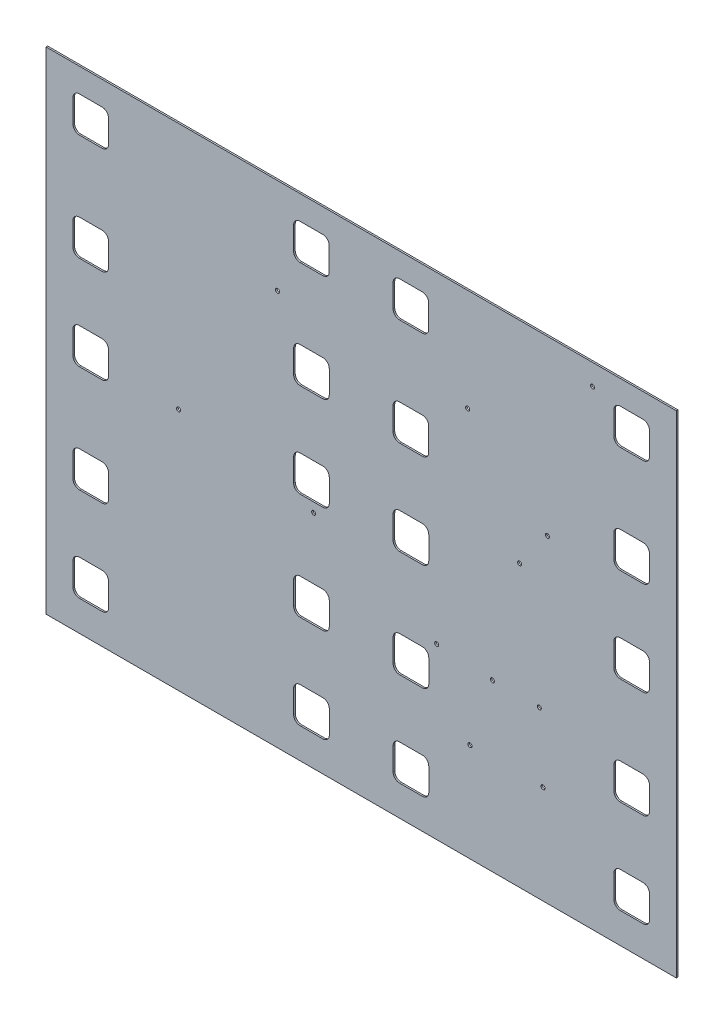
SolidWorks part; units mm, degrees
material "ABS"
ref_plane "X-Y Datum" through (0, 0, 0) normal (0, 0, 1) x (1, 0, 0)
ref_plane "X-Z Datum" through (0, 0, 0) normal (0, 1, 0) x (1, 0, 0)
ref_plane "Y-Z Datum" through (0, 0, 0) normal (1, 0, 0) x (0, 0, -1)
sketch "Sketch9" plane through (0, 0, 0) normal (0, 0, 1) x (1, 0, 0)
  line L0 (-82.7559, -182.5893) -> (-82.7583, -160.1613) construction
  line L1 (-89.109, -153.8119) -> (-111.537, -153.8143) construction
  line L2 (-117.8863, -160.165) -> (-117.8839, -182.593) construction
  line L3 (-111.5333, -188.9423) -> (-89.1053, -188.9399) construction
  line L4 (476.934, -311.4483) -> (476.8831, 172.8027)
  line L5 (476.8831, 172.8027) -> (-144.3755, 172.7375)
  line L6 (-144.3755, 172.7375) -> (-144.3246, -311.5135)
  line L7 (-144.3246, -311.5135) -> (476.934, -311.4483)
  line L8 (476.934, -311.4483) -> (476.8831, 172.8027)
  line L9 (476.8831, 172.8027) -> (-144.3755, 172.7375)
  line L10 (-144.3755, 172.7375) -> (-144.3246, -311.5135)
  line L11 (-144.3246, -311.5135) -> (476.934, -311.4483)
  line L12 (-111.5443, -83.8117) -> (-89.1163, -83.8093) construction
  line L13 (-82.767, -77.4587) -> (-82.7693, -55.0307) construction
  line L14 (-89.12, -48.6813) -> (-111.548, -48.6837) construction
  line L15 (-117.8973, -55.0344) -> (-117.895, -77.4624) construction
  line L16 (-82.7877, 120.2549) -> (-82.7901, 142.6829) construction
  line L17 (-89.1408, 149.0323) -> (-111.5688, 149.0299) construction
  line L18 (-117.9181, 142.6792) -> (-117.9157, 120.2512) construction
  line L19 (-111.5651, 113.9019) -> (-89.1371, 113.9043) construction
  line L20 (-111.554, 8.7713) -> (-89.126, 8.7737) construction
  line L21 (-117.9071, 37.5486) -> (-117.9047, 15.1206) construction
  line L22 (-89.1297, 43.9017) -> (-111.5577, 43.8993) construction
  line L23 (-82.7767, 15.1243) -> (-82.7791, 37.5523) construction
  line L24 (-82.7559, -182.5893) -> (-82.7583, -160.1613)
  line L25 (-89.109, -153.8119) -> (-111.537, -153.8143)
  line L26 (-117.8863, -160.165) -> (-117.8839, -182.593)
  line L27 (-111.5333, -188.9423) -> (-89.1053, -188.9399)
  line L28 (-111.5443, -83.8117) -> (-89.1163, -83.8093)
  line L29 (-82.767, -77.4587) -> (-82.7693, -55.0307)
  line L30 (-89.12, -48.6813) -> (-111.548, -48.6837)
  line L31 (-117.8973, -55.0344) -> (-117.895, -77.4624)
  line L32 (-82.7877, 120.2549) -> (-82.7901, 142.6829)
  line L33 (-89.1408, 149.0323) -> (-111.5688, 149.0299)
  line L34 (-117.9181, 142.6792) -> (-117.9157, 120.2512)
  line L35 (-111.5651, 113.9019) -> (-89.1371, 113.9043)
  line L36 (-111.554, 8.7713) -> (-89.126, 8.7737)
  line L37 (-117.9071, 37.5486) -> (-117.9047, 15.1206)
  line L38 (-89.1297, 43.9017) -> (-111.5577, 43.8993)
  line L39 (-82.7767, 15.1243) -> (-82.7791, 37.5523)
  line L40 (-82.7462, -275.1723) -> (-82.7486, -252.7443) construction
  line L41 (-89.0992, -246.3949) -> (-111.5272, -246.3973) construction
  line L42 (-117.8766, -252.748) -> (-117.8742, -275.176) construction
  line L43 (-111.5235, -281.5253) -> (-89.0955, -281.5229) construction
  line L44 (-82.7462, -275.1723) -> (-82.7486, -252.7443)
  line L45 (-89.0992, -246.3949) -> (-111.5272, -246.3973)
  line L46 (-117.8766, -252.748) -> (-117.8742, -275.176)
  line L47 (-111.5235, -281.5253) -> (-89.0955, -281.5229)
  arc A0 (-89.1053, -188.9399) -> (-82.7559, -182.5893) centre (-89.1059, -182.5899) ccw construction
  arc A1 (-82.7583, -160.1613) -> (-89.109, -153.8119) centre (-89.1083, -160.1619) ccw construction
  arc A2 (-111.537, -153.8143) -> (-117.8863, -160.165) centre (-111.5363, -160.1643) ccw construction
  arc A3 (-117.8839, -182.593) -> (-111.5333, -188.9423) centre (-111.5339, -182.5923) ccw construction
  arc A4 (-89.1163, -83.8093) -> (-82.767, -77.4587) centre (-89.117, -77.4593) ccw construction
  arc A5 (-82.7693, -55.0307) -> (-89.12, -48.6813) centre (-89.1193, -55.0313) ccw construction
  arc A6 (-111.548, -48.6837) -> (-117.8973, -55.0344) centre (-111.5473, -55.0337) ccw construction
  arc A7 (-117.895, -77.4624) -> (-111.5443, -83.8117) centre (-111.545, -77.4617) ccw construction
  arc A8 (-89.1371, 113.9043) -> (-82.7877, 120.2549) centre (-89.1377, 120.2543) ccw construction
  arc A9 (-82.7901, 142.6829) -> (-89.1408, 149.0323) centre (-89.1401, 142.6823) ccw construction
  arc A10 (-111.5688, 149.0299) -> (-117.9181, 142.6792) centre (-111.5681, 142.6799) ccw construction
  arc A11 (-117.9157, 120.2512) -> (-111.5651, 113.9019) centre (-111.5657, 120.2519) ccw construction
  arc A12 (-82.7791, 37.5523) -> (-89.1297, 43.9017) centre (-89.1291, 37.5517) ccw construction
  arc A13 (-89.126, 8.7737) -> (-82.7767, 15.1243) centre (-89.1267, 15.1237) ccw construction
  arc A14 (-117.9047, 15.1206) -> (-111.554, 8.7713) centre (-111.5547, 15.1213) ccw construction
  arc A15 (-111.5577, 43.8993) -> (-117.9071, 37.5486) centre (-111.5571, 37.5493) ccw construction
  arc A16 (-89.1053, -188.9399) -> (-82.7559, -182.5893) centre (-89.1059, -182.5899) ccw
  arc A17 (-82.7583, -160.1613) -> (-89.109, -153.8119) centre (-89.1083, -160.1619) ccw
  arc A18 (-111.537, -153.8143) -> (-117.8863, -160.165) centre (-111.5363, -160.1643) ccw
  arc A19 (-117.8839, -182.593) -> (-111.5333, -188.9423) centre (-111.5339, -182.5923) ccw
  arc A20 (-89.1163, -83.8093) -> (-82.767, -77.4587) centre (-89.117, -77.4593) ccw
  arc A21 (-82.7693, -55.0307) -> (-89.12, -48.6813) centre (-89.1193, -55.0313) ccw
  arc A22 (-111.548, -48.6837) -> (-117.8973, -55.0344) centre (-111.5473, -55.0337) ccw
  arc A23 (-117.895, -77.4624) -> (-111.5443, -83.8117) centre (-111.545, -77.4617) ccw
  arc A24 (-89.1371, 113.9043) -> (-82.7877, 120.2549) centre (-89.1377, 120.2543) ccw
  arc A25 (-82.7901, 142.6829) -> (-89.1408, 149.0323) centre (-89.1401, 142.6823) ccw
  arc A26 (-111.5688, 149.0299) -> (-117.9181, 142.6792) centre (-111.5681, 142.6799) ccw
  arc A27 (-117.9157, 120.2512) -> (-111.5651, 113.9019) centre (-111.5657, 120.2519) ccw
  arc A28 (-82.7791, 37.5523) -> (-89.1297, 43.9017) centre (-89.1291, 37.5517) ccw
  arc A29 (-89.126, 8.7737) -> (-82.7767, 15.1243) centre (-89.1267, 15.1237) ccw
  arc A30 (-117.9047, 15.1206) -> (-111.554, 8.7713) centre (-111.5547, 15.1213) ccw
  arc A31 (-111.5577, 43.8993) -> (-117.9071, 37.5486) centre (-111.5571, 37.5493) ccw
  arc A32 (-89.0955, -281.5229) -> (-82.7462, -275.1723) centre (-89.0962, -275.1729) ccw construction
  arc A33 (-111.5272, -246.3973) -> (-117.8766, -252.748) centre (-111.5266, -252.7473) ccw construction
  arc A34 (-117.8742, -275.176) -> (-111.5235, -281.5253) centre (-111.5242, -275.1753) ccw construction
  arc A35 (-89.0955, -281.5229) -> (-82.7462, -275.1723) centre (-89.0962, -275.1729) ccw
  arc A36 (-111.5272, -246.3973) -> (-117.8766, -252.748) centre (-111.5266, -252.7473) ccw
  arc A37 (-117.8742, -275.176) -> (-111.5235, -281.5253) centre (-111.5242, -275.1753) ccw
  arc A38 (-82.7486, -252.7443) -> (-89.0992, -246.3949) centre (-89.0986, -252.7449) ccw construction
  arc A39 (-82.7486, -252.7443) -> (-89.0992, -246.3949) centre (-89.0986, -252.7449) ccw
  dimension "D1" = 0
extrude "Boss-Extrude2" add sketch "Sketch9" along normal blind 1.5875 contours L10 L11 L8 L9 A39 L44 A35 L47 A37 L46 A36 L45 A31 L38 A28 L39 A29 L36 A30 L37 A27 L34 A26 L33 A25 L32 A24 L35 A23 L31 A22 L30 A21 L29 A20 L28 A19 L26 A18 L25 A17 L24 A16 L27 | L44 A39 L45 A36 L46 A37 L47 A35 | L26 A19 L27 A16 L24 A17 L25 A18 | L38 A31 L37 A30 L36 A29 L39 A28 | L34 A27 L35 A24 L32 A25 L33 A26 | L31 A23 L28 A20 L29 A21 L30 A22
sketch "Sketch10" plane through (0, 0, 1.5875) normal (0, 0, 1) x (1, 0, 0)
  line L4 (476.934, -311.4483) -> (476.8831, 172.8027)
  line L5 (476.8831, 172.8027) -> (-144.3755, 172.7375)
  line L6 (-144.3755, 172.7375) -> (-144.3246, -311.5135)
  line L7 (-144.3246, -311.5135) -> (476.934, -311.4483)
  line L8 (476.934, -311.4483) -> (476.8831, 172.8027)
  line L9 (476.8831, 172.8027) -> (-144.3755, 172.7375)
  line L10 (-144.3755, 172.7375) -> (-144.3246, -311.5135)
  line L11 (-144.3246, -311.5135) -> (476.934, -311.4483)
  line L12 (-117.8863, -160.165) -> (-117.8839, -182.593)
  line L13 (-111.5333, -188.9423) -> (-89.1053, -188.9399)
  line L14 (-82.7559, -182.5893) -> (-82.7583, -160.1613)
  line L15 (-89.109, -153.8119) -> (-111.537, -153.8143)
  line L16 (-117.8863, -160.165) -> (-117.8839, -182.593)
  line L17 (-111.5333, -188.9423) -> (-89.1053, -188.9399)
  line L18 (-82.7559, -182.5893) -> (-82.7583, -160.1613)
  line L19 (-89.109, -153.8119) -> (-111.537, -153.8143)
  line L20 (-117.8766, -252.748) -> (-117.8742, -275.176)
  line L21 (-89.0992, -246.3949) -> (-111.5272, -246.3973)
  line L22 (-82.7462, -275.1723) -> (-82.7486, -252.7443)
  line L23 (-111.5235, -281.5253) -> (-89.0955, -281.5229)
  line L24 (-117.8766, -252.748) -> (-117.8742, -275.176)
  line L25 (-89.0992, -246.3949) -> (-111.5272, -246.3973)
  line L26 (-82.7462, -275.1723) -> (-82.7486, -252.7443)
  line L27 (-111.5235, -281.5253) -> (-89.0955, -281.5229)
  line L28 (-89.12, -48.6813) -> (-111.548, -48.6837)
  line L29 (-117.8973, -55.0344) -> (-117.895, -77.4624)
  line L30 (-111.5443, -83.8117) -> (-89.1163, -83.8093)
  line L31 (-82.767, -77.4587) -> (-82.7693, -55.0307)
  line L32 (-89.12, -48.6813) -> (-111.548, -48.6837)
  line L33 (-117.8973, -55.0344) -> (-117.895, -77.4624)
  line L34 (-111.5443, -83.8117) -> (-89.1163, -83.8093)
  line L35 (-82.767, -77.4587) -> (-82.7693, -55.0307)
  line L36 (-82.7877, 120.2549) -> (-82.7901, 142.6829)
  line L37 (-111.5651, 113.9019) -> (-89.1371, 113.9043)
  line L38 (-117.9181, 142.6792) -> (-117.9157, 120.2512)
  line L39 (-89.1408, 149.0323) -> (-111.5688, 149.0299)
  line L40 (-82.7877, 120.2549) -> (-82.7901, 142.6829)
  line L41 (-111.5651, 113.9019) -> (-89.1371, 113.9043)
  line L42 (-117.9181, 142.6792) -> (-117.9157, 120.2512)
  line L43 (-89.1408, 149.0323) -> (-111.5688, 149.0299)
  line L44 (-111.554, 8.7713) -> (-89.126, 8.7737)
  line L45 (-82.7767, 15.1243) -> (-82.7791, 37.5523)
  line L46 (-89.1297, 43.9017) -> (-111.5577, 43.8993)
  line L47 (-117.9071, 37.5486) -> (-117.9047, 15.1206)
  line L48 (-111.554, 8.7713) -> (-89.126, 8.7737)
  line L49 (-82.7767, 15.1243) -> (-82.7791, 37.5523)
  line L50 (-89.1297, 43.9017) -> (-111.5577, 43.8993)
  line L51 (-117.9071, 37.5486) -> (-117.9047, 15.1206)
  arc A4 (-117.8839, -182.593) -> (-111.5333, -188.9423) centre (-111.5339, -182.5923) ccw
  arc A5 (-89.1053, -188.9399) -> (-82.7559, -182.5893) centre (-89.1059, -182.5899) ccw
  arc A6 (-82.7583, -160.1613) -> (-89.109, -153.8119) centre (-89.1083, -160.1619) ccw
  arc A7 (-111.537, -153.8143) -> (-117.8863, -160.165) centre (-111.5363, -160.1643) ccw
  arc A8 (-117.8839, -182.593) -> (-111.5333, -188.9423) centre (-111.5339, -182.5923) ccw
  arc A9 (-89.1053, -188.9399) -> (-82.7559, -182.5893) centre (-89.1059, -182.5899) ccw
  arc A10 (-82.7583, -160.1613) -> (-89.109, -153.8119) centre (-89.1083, -160.1619) ccw
  arc A11 (-111.537, -153.8143) -> (-117.8863, -160.165) centre (-111.5363, -160.1643) ccw
  arc A12 (-111.5272, -246.3973) -> (-117.8766, -252.748) centre (-111.5266, -252.7473) ccw
  arc A13 (-82.7486, -252.7443) -> (-89.0992, -246.3949) centre (-89.0986, -252.7449) ccw
  arc A14 (-89.0955, -281.5229) -> (-82.7462, -275.1723) centre (-89.0962, -275.1729) ccw
  arc A15 (-117.8742, -275.176) -> (-111.5235, -281.5253) centre (-111.5242, -275.1753) ccw
  arc A16 (-111.5272, -246.3973) -> (-117.8766, -252.748) centre (-111.5266, -252.7473) ccw
  arc A17 (-82.7486, -252.7443) -> (-89.0992, -246.3949) centre (-89.0986, -252.7449) ccw
  arc A18 (-89.0955, -281.5229) -> (-82.7462, -275.1723) centre (-89.0962, -275.1729) ccw
  arc A19 (-117.8742, -275.176) -> (-111.5235, -281.5253) centre (-111.5242, -275.1753) ccw
  arc A20 (-111.548, -48.6837) -> (-117.8973, -55.0344) centre (-111.5473, -55.0337) ccw
  arc A21 (-117.895, -77.4624) -> (-111.5443, -83.8117) centre (-111.545, -77.4617) ccw
  arc A22 (-89.1163, -83.8093) -> (-82.767, -77.4587) centre (-89.117, -77.4593) ccw
  arc A23 (-82.7693, -55.0307) -> (-89.12, -48.6813) centre (-89.1193, -55.0313) ccw
  arc A24 (-111.548, -48.6837) -> (-117.8973, -55.0344) centre (-111.5473, -55.0337) ccw
  arc A25 (-117.895, -77.4624) -> (-111.5443, -83.8117) centre (-111.545, -77.4617) ccw
  arc A26 (-89.1163, -83.8093) -> (-82.767, -77.4587) centre (-89.117, -77.4593) ccw
  arc A27 (-82.7693, -55.0307) -> (-89.12, -48.6813) centre (-89.1193, -55.0313) ccw
  arc A28 (-89.1371, 113.9043) -> (-82.7877, 120.2549) centre (-89.1377, 120.2543) ccw
  arc A29 (-117.9157, 120.2512) -> (-111.5651, 113.9019) centre (-111.5657, 120.2519) ccw
  arc A30 (-111.5688, 149.0299) -> (-117.9181, 142.6792) centre (-111.5681, 142.6799) ccw
  arc A31 (-82.7901, 142.6829) -> (-89.1408, 149.0323) centre (-89.1401, 142.6823) ccw
  arc A32 (-89.1371, 113.9043) -> (-82.7877, 120.2549) centre (-89.1377, 120.2543) ccw
  arc A33 (-117.9157, 120.2512) -> (-111.5651, 113.9019) centre (-111.5657, 120.2519) ccw
  arc A34 (-111.5688, 149.0299) -> (-117.9181, 142.6792) centre (-111.5681, 142.6799) ccw
  arc A35 (-82.7901, 142.6829) -> (-89.1408, 149.0323) centre (-89.1401, 142.6823) ccw
  arc A36 (-89.126, 8.7737) -> (-82.7767, 15.1243) centre (-89.1267, 15.1237) ccw
  arc A37 (-82.7791, 37.5523) -> (-89.1297, 43.9017) centre (-89.1291, 37.5517) ccw
  arc A38 (-111.5577, 43.8993) -> (-117.9071, 37.5486) centre (-111.5571, 37.5493) ccw
  arc A39 (-117.9047, 15.1206) -> (-111.554, 8.7713) centre (-111.5547, 15.1213) ccw
  arc A40 (-89.126, 8.7737) -> (-82.7767, 15.1243) centre (-89.1267, 15.1237) ccw
  arc A41 (-82.7791, 37.5523) -> (-89.1297, 43.9017) centre (-89.1291, 37.5517) ccw
  arc A42 (-111.5577, 43.8993) -> (-117.9071, 37.5486) centre (-111.5571, 37.5493) ccw
  arc A43 (-117.9047, 15.1206) -> (-111.554, 8.7713) centre (-111.5547, 15.1213) ccw
  dimension "D1" = 0
  dimension "D2" = 0
  dimension "D3" = 0
  dimension "D4" = 0
  dimension "D5" = 0
  dimension "D6" = 0
extrude "Cut-Extrude6" cut sketch "Sketch10" against normal through all contours L40 A35 L43 A34 L42 A33 L41 A32 | L51 A43 L48 A40 L49 A41 L50 A42 | L35 A27 L32 A24 L33 A25 L34 A26 | L19 A11 L16 A8 L17 A9 L18 A10 | L24 A19 L27 A18 L26 A17 L25 A16
pattern_linear "LPattern2" count 2 spacing 217.5764 along (1, 0.0001, 0) of "Cut-Extrude6"
ref_plane "Plane1" through (166.272, 0.0175, 0) normal (-1, -0.0001, 0) x (0, 0, 1)
mirror "Mirror1" about plane through (166.272, 0.0175, 0) normal (-1, -0.0001, 0) of "LPattern2", "Cut-Extrude6"
sketch "Sketch11" plane through (0, 0, 1.5875) normal (0, 0, 1) x (1, 0, 0)
  circle A3 centre (295.6543, -147.9548) radius 1.9939
  circle A5 centre (295.6543, -147.9548) radius 1.9939
  circle A7 centre (394.3353, 152.1565) radius 1.9939
  circle A9 centre (394.3353, 152.1565) radius 1.9939
  circle A11 centre (271.1937, 71.8561) radius 1.9939
  circle A13 centre (271.1937, 71.8561) radius 1.9939
  circle A15 centre (83.7969, 78.6239) radius 1.9939
  circle A17 centre (83.7969, 78.6239) radius 1.9939
  circle A19 centre (-13.7373, -71.3863) radius 1.9939
  circle A21 centre (-13.7373, -71.3863) radius 1.9939
  circle A23 centre (349.9245, 2.4389) radius 1.9939
  circle A44 centre (349.9245, 2.4389) radius 1.9939
  circle A45 centre (322.4284, -34.688) radius 1.9939
  circle A46 centre (322.4284, -34.688) radius 1.9939
  circle A47 centre (341.8543, -147.95) radius 1.9939
  circle A48 centre (341.8543, -147.95) radius 1.9939
  circle A49 centre (345.5113, -214.3496) radius 1.9939
  circle A50 centre (345.5113, -214.3496) radius 1.9939
  circle A51 centre (119.4061, -93.0712) radius 1.9939
  circle A52 centre (119.4061, -93.0712) radius 1.9939
  circle A53 centre (240.6965, -144.4935) radius 1.9939
  circle A54 centre (240.6965, -144.4935) radius 1.9939
  circle A55 centre (273.5113, -214.3572) radius 1.9939
  circle A56 centre (273.5113, -214.3572) radius 1.9939
  dimension "D1" = 0
  dimension "D2" = 0
  dimension "D3" = 0
  dimension "D4" = 0
  dimension "D5" = 0
  dimension "D6" = 0
  dimension "D7" = 0
  dimension "D8" = 0
  dimension "D9" = 0
  dimension "D10" = 0
  dimension "D11" = 0
  dimension "D12" = 0
extrude "Cut-Extrude7" cut sketch "Sketch11" against normal through all
